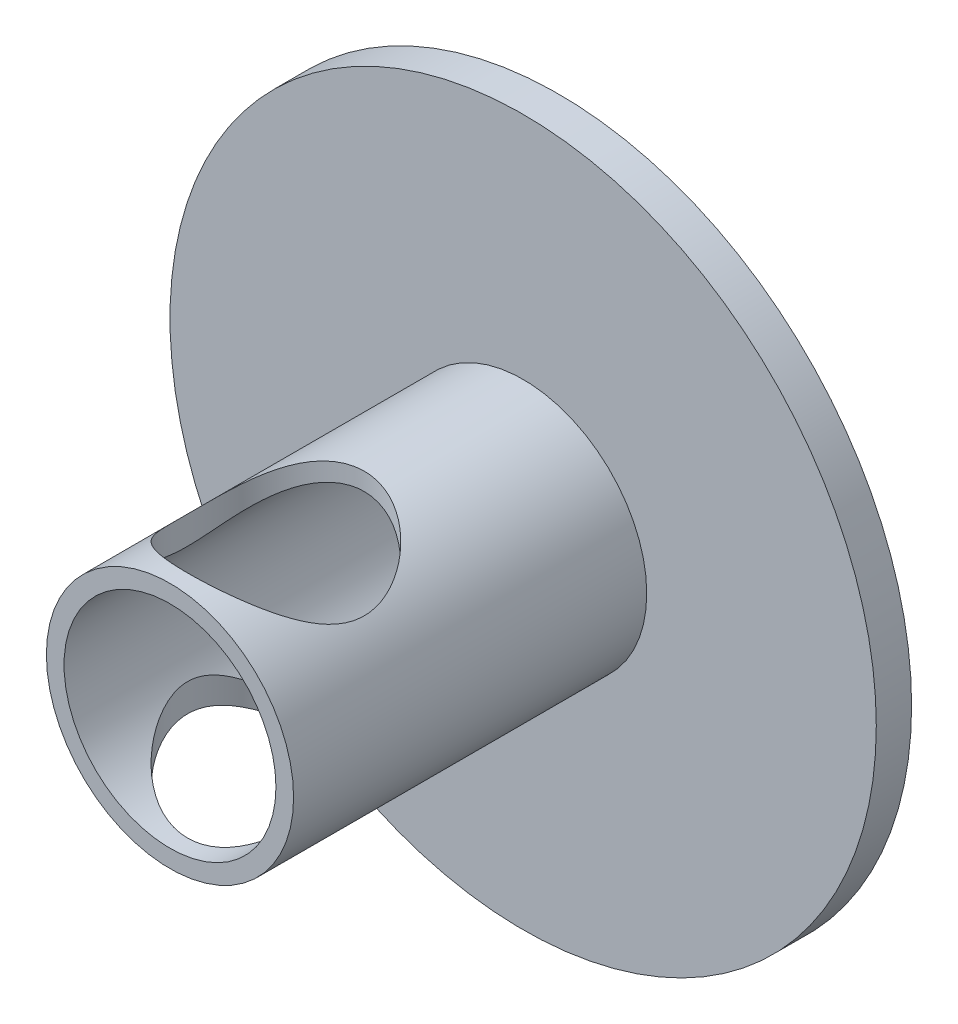
SolidWorks part; units mm, degrees
material "PLA"
ref_plane "Alzado" through (0, 0, 0) normal (0, 0, 1) x (1, 0, 0)
ref_plane "Planta" through (0, 0, 0) normal (0, 1, 0) x (1, 0, 0)
ref_plane "Vista lateral" through (0, 0, 0) normal (1, 0, 0) x (0, 0, -1)
sketch "Croquis1" plane through (0, 0, 0) normal (0, 0, 1) x (1, 0, 0)
  circle A0 centre (0, 0) radius 10
extrude "Saliente-Extruir1" add sketch "Croquis1" along normal blind 1
sketch "Croquis2" plane through (0, 0, 1) normal (0, 0, 1) x (1, 0, 0)
  circle A0 centre (0, 0) radius 3.5
extrude "Saliente-Extruir2" add sketch "Croquis2" along normal blind 10
sketch "Croquis3" plane through (0, 0, 11) normal (0, 0, 1) x (1, 0, 0)
  circle A0 centre (0, 0) radius 3
extrude "Cortar-Extruir1" cut sketch "Croquis3" against normal blind 10
sketch "Croquis4" plane through (0, 0, 0) normal (0, 1, 0) x (1, 0, 0)
  line L0 (0, 0) -> (0, -8) construction
  line L1 (0, -8) -> (2.5, -8) construction
  line L2 (1.25, -8) -> (1.25, -5.8349) construction
  line L3 (1.25, -6.9175) -> (2.2535, -6.9175) construction
  circle A0 centre (0, -8) radius 2.5 construction
  arc A1 (1.25, -5.8349) -> (-1.25, -5.8349) centre (0, -8) ccw
  arc A2 (2.2535, -6.9175) -> (2.2535, -9.0825) centre (0, -8) cw
  arc A3 (1.25, -10.1651) -> (-1.25, -10.1651) centre (0, -8) cw
  arc A4 (-2.2535, -6.9175) -> (-2.2535, -9.0825) centre (0, -8) ccw
  arc A5 (-2.2535, -6.9175) -> (-1.25, -5.8349) centre (0, -8) cw
  arc A6 (-2.2535, -9.0825) -> (-1.25, -10.1651) centre (0, -8) ccw
  arc A7 (1.25, -10.1651) -> (2.2535, -9.0825) centre (0, -8) ccw
  arc A8 (1.25, -5.8349) -> (2.2535, -6.9175) centre (0, -8) cw
extrude "Cortar-Extruir2" cut sketch "Croquis4" against normal blind 10
mirror "Simetría1" about plane through (0, 0, 0) normal (0, 1, 0) of "Cortar-Extruir2"
